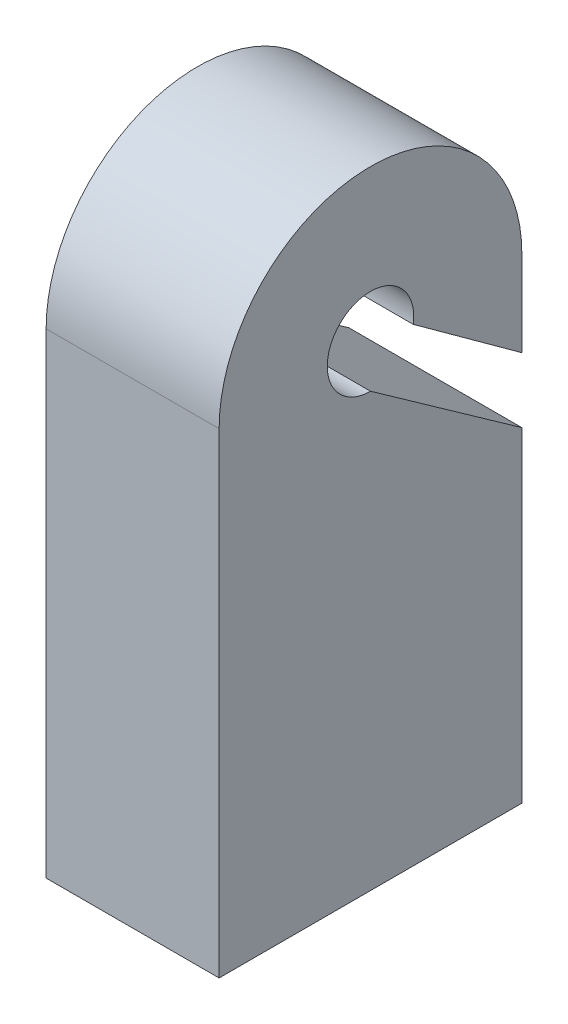
SolidWorks part; units mm, degrees
ref_plane "Front Plane" through (0, 0, 0) normal (0, 0, 1) x (1, 0, 0)
ref_plane "Top Plane" through (0, 0, 0) normal (0, 1, 0) x (1, 0, 0)
ref_plane "Right Plane" through (0, 0, 0) normal (1, 0, 0) x (0, 0, -1)
sketch "Sketch1" plane through (0, 0, 0) normal (1, 0, 0) x (0, 0, -1)
  line L0 (-0.25, 4.2541) -> (-0.25, 1.7459) construction
  line L1 (1.5, -2.5) -> (-2, -2.5)
  line L2 (1.5, -2.5) -> (1.5, 0.1935)
  line L4 (-2, -2.5) -> (-2, 3)
  line L5 (-2, -2.5) -> (1.5, 3) construction
  line L6 (-2, 3) -> (1.5, -2.5) construction
  line L7 (1.5, 2.0106) -> (1.5, 3)
  line L9 (1.5, 0.5444) -> (1.5, 1.2606)
  line L10 (0.244, 2.9225) -> (1.5, 2.0106)
  line L11 (1.5, 0.1935) -> (1.5, 1.2606)
  line L12 (1.5, 1.2606) -> (-0.25, 2.5)
  arc A0 (0.244, 2.9225) -> (-0.25, 2.5) centre (-0.25, 3) ccw
  arc A2 (1.5, 3) -> (-2, 3) centre (-0.25, 3) ccw
  point P0 (0, 0)
  dimension "D3" = 1
  dimension "D4" = 1.75
  dimension "D1" = 5.5
  dimension "D2" = 3.5
  dimension "D5" = 0.75
  dimension "D6" = 0.65
extrude "Boss-Extrude1" add sketch "Sketch1" along normal blind 2
